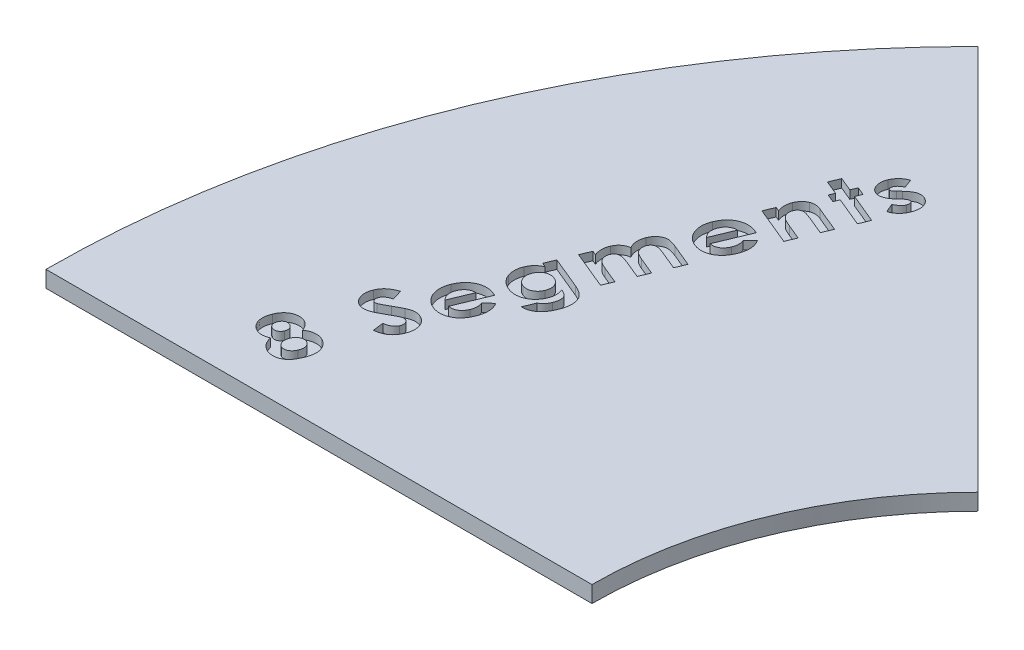
SolidWorks part; units mm, degrees
ref_plane "Front Plane" through (0, 0, 0) normal (0, 0, 1) x (1, 0, 0)
ref_plane "Top Plane" through (0, 0, 0) normal (0, 1, 0) x (1, 0, 0)
ref_plane "Right Plane" through (0, 0, 0) normal (1, 0, 0) x (0, 0, -1)
sketch "Sketch1" plane through (0, 0, 0) normal (0, 1, 0) x (1, 0, 0)
  line L0 (0, 0) -> (105.2102, 0)
  line L1 (127, 52.6051) -> (52.6051, 127)
  arc A0 (105.2102, 0) -> (127, 52.6051) centre (179.6051, 0) cw
  arc A1 (0, 0) -> (52.6051, 127) centre (179.6051, 0) cw
  dimension "D1" = 45
  dimension "D2" = 127
  dimension "D3" = 127
extrude "Boss-Extrude1" add sketch "Sketch1" along normal blind 3.175
sketch "Sketch2" plane through (0, 3.175, 0) normal (0, 1, 0) x (1, 0, 0)
  line L0 (35.052, 0) -> (77.3906, 102.2145) construction
  line L1 (0, 0) -> (105.2102, 0) construction
  line L2 (127, 52.6051) -> (52.6051, 127) construction
  text T0 "<b>8 Segments</b>" font "Century Gothic" height in points 40
  dimension "D1" = 35.052
  dimension "D2" = 35.052
extrude "Cut-Extrude1" cut sketch "Sketch2" against normal blind 1.5875
